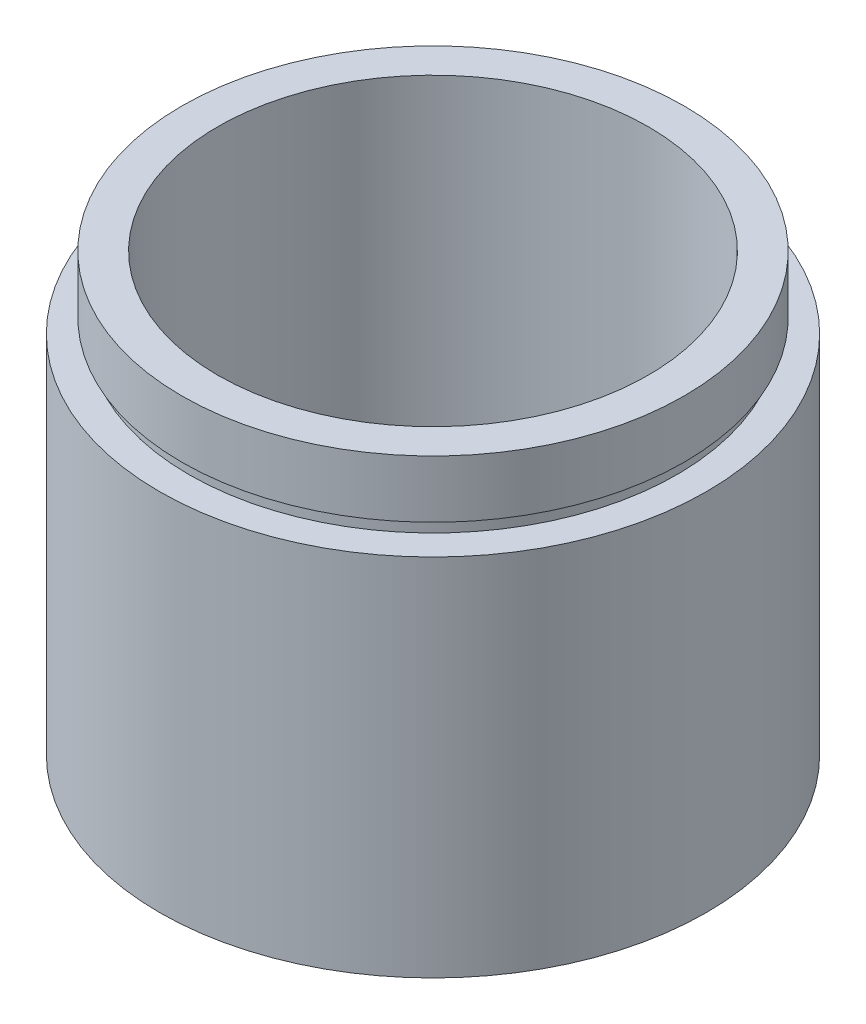
SolidWorks part; units mm, degrees
ref_plane "前视基准面" through (0, 0, 0) normal (0, 0, 1) x (1, 0, 0)
ref_plane "上视基准面" through (0, 0, 0) normal (0, 1, 0) x (1, 0, 0)
ref_plane "右视基准面" through (0, 0, 0) normal (1, 0, 0) x (0, 0, -1)
sketch "草图1" plane through (0, 0, 0) normal (0, 0, 1) x (1, 0, 0)
  line L0 (0, 161.3762) -> (0, 0) construction
  line L1 (141.7365, 0) -> (-131.7984, 0) construction
  line L2 (19.05, 0) -> (19.05, 25.4)
  line L3 (17, 4.5) -> (17.6, 4.5)
  line L4 (17, 0) -> (19.05, 0)
  line L5 (17.6, 4.5) -> (17.6, 5.5)
  line L6 (15, 5.5) -> (15, 30.4)
  line L7 (17, 4.5) -> (17, 0)
  line L8 (17.6, 5.5) -> (15, 5.5)
  line L9 (17, 26.4) -> (17, 25.4)
  line L10 (19.05, 25.4) -> (17, 25.4)
  line L11 (17.5, 26.4) -> (17.5, 30.4)
  line L12 (17, 26.4) -> (17.5, 26.4)
  line L13 (17.5, 30.4) -> (15, 30.4)
  dimension "D2" = 19.05
  dimension "D3" = 17.6
  dimension "D4" = 15
  dimension "D5" = 17
  dimension "D6" = 17.5
  dimension "D7" = 1
  dimension "D8" = 25.4
  dimension "D9" = 5
  dimension "D10" = 1
  dimension "D11" = 17
revolve "旋转1" add sketch "草图1" angle 360 about L0
cosmetic thread "装饰螺纹线1"
cosmetic thread "装饰螺纹线2"
cosmetic thread "装饰螺纹线3"
